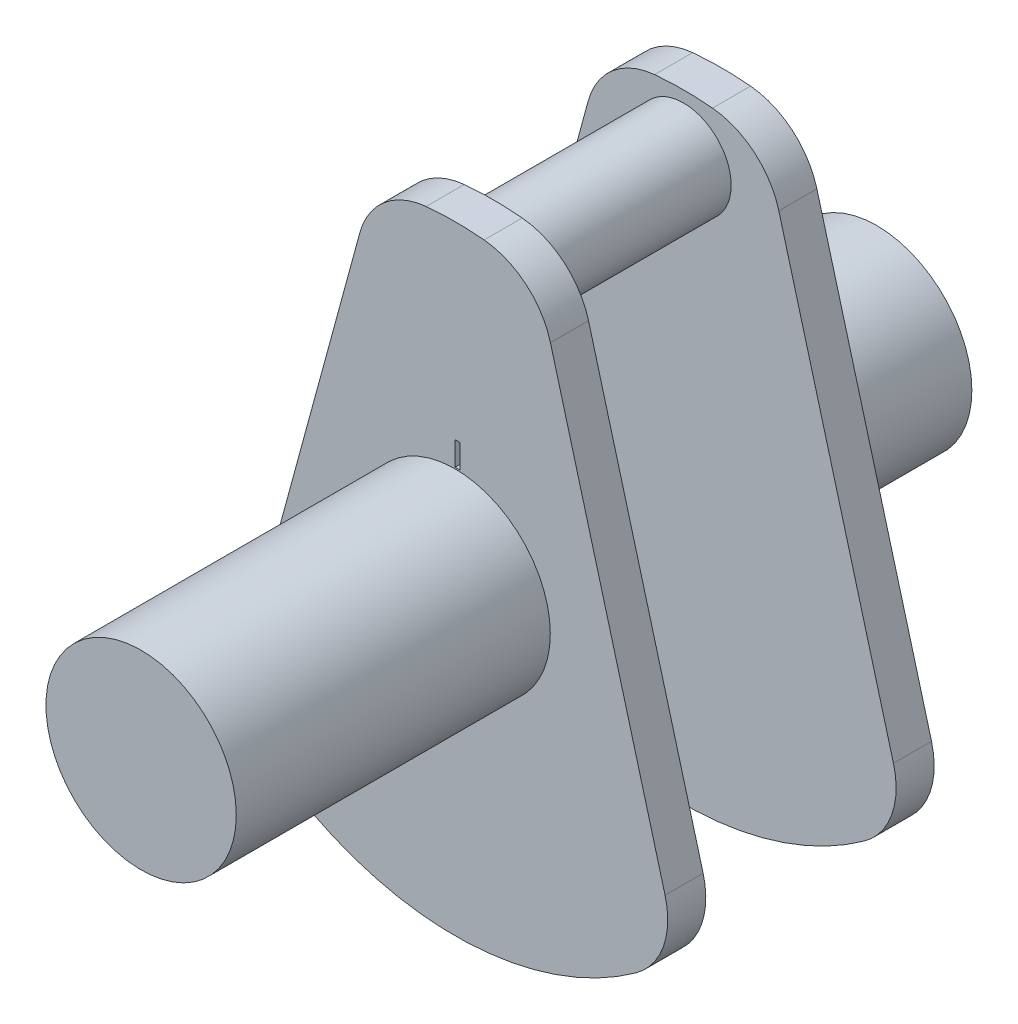
SolidWorks part; units mm, degrees
ref_plane "Front Plane" through (0, 0, 0) normal (0, 0, 1) x (1, 0, 0)
ref_plane "Top Plane" through (0, 0, 0) normal (0, 1, 0) x (1, 0, 0)
ref_plane "Right Plane" through (0, 0, 0) normal (1, 0, 0) x (0, 0, -1)
sketch "Sketch2" plane through (0, 0, 0) normal (0, 0, 1) x (1, 0, 0)
  line L0 (0, 6.5) -> (0, -6.5) construction
  line L1 (-2.0028, 5.2986) -> (-4.4119, -3.5528)
  line L2 (2.0028, 5.2986) -> (4.4119, -3.5528)
  arc A0 (-3.8045, -5.2703) -> (3.8045, -5.2703) centre (0, 0) ccw
  arc A1 (0.6089, 6.4714) -> (-0.6089, 6.4714) centre (0, 0) ccw
  arc A2 (2.0028, 5.2986) -> (0.6089, 6.4714) centre (0.459, 4.8785) ccw
  arc A3 (-2.0028, 5.2986) -> (-0.6089, 6.4714) centre (-0.459, 4.8785) cw
  arc A4 (4.4119, -3.5528) -> (3.8045, -5.2703) centre (2.868, -3.973) cw
  arc A5 (-4.4119, -3.5528) -> (-3.8045, -5.2703) centre (-2.868, -3.973) ccw
  point P10 (1.7405, 6.2626)
  point P13 (-1.7405, 6.2626)
  point P17 (4.6742, -4.5168)
  point P20 (-4.6742, -4.5168)
  dimension "D1" = 13
  dimension "D4" = 1.6
  dimension "D5" = 1.6
  dimension "D2" = 30.45
  dimension "D3" = 0.918
extrude "Boss-Extrude1" add sketch "Sketch2" along normal blind 0.8
sketch "Sketch3" plane through (0, 0, 0.8) normal (0, 0, 1) x (1, 0, 0)
  line L0 (0, 6.5) -> (0, 5.26) construction
  arc A0 (0.6089, 6.4714) -> (-0.6089, 6.4714) centre (0, 0) ccw construction
  circle A1 centre (0, 5.26) radius 1
  dimension "D1" = 2
  dimension "D2" = 5.26
extrude "Boss-Extrude2" add sketch "Sketch3" along normal blind 2
sketch "Sketch4" plane through (0, 0, 0) normal (0, 0, -1) x (-1, 0, 0)
  circle A0 centre (0, 0) radius 2
  dimension "D1" = 4
extrude "Boss-Extrude3" add sketch "Sketch4" along normal blind 3.26
mirror "Mirror1" about plane through (0, 5.26, 2.8) normal (0, 0, 1) of bodies 103
sketch "Sketch5" plane through (0, 0, 8.86) normal (0, 0, 1) x (1, 0, 0)
  circle A1 centre (0, 0) radius 2
  circle A2 centre (0, 0) radius 2
  dimension "D1" = 0
extrude "Boss-Extrude4" add sketch "Sketch5" along normal blind 3.34
sketch "Sketch6" plane through (0, 0, 5.6) normal (0, 0, 1) x (1, 0, 0)
  line L0 (0, 0) -> (0, 5.1578) construction
  line L2 (0, 2.5306) -> (0.1, 2.5306)
  line L3 (0, 2.5306) -> (0, 2.0306)
  line L4 (0, 2.0306) -> (0.1, 2.0306)
  line L5 (0.1, 2.5306) -> (0.1, 2.0306)
  line L6 (0, 2.5306) -> (0.1, 2.0306) construction
  line L7 (0, 2.0306) -> (0.1, 2.5306) construction
  point P7 (0.05, 2.2806)
  dimension "D1" = 0.1
  dimension "D2" = 0.5
extrude "Cut-Extrude1" cut sketch "Sketch6" against normal blind 0.1
